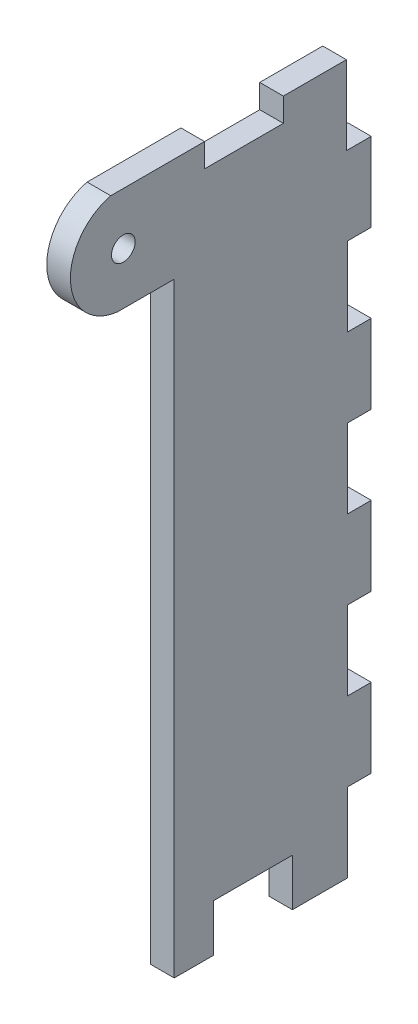
SolidWorks part; units mm, degrees
ref_plane "Front Plane" through (0, 0, 0) normal (0, 0, 1) x (1, 0, 0)
ref_plane "Top Plane" through (0, 0, 0) normal (0, 1, 0) x (1, 0, 0)
ref_plane "Right Plane" through (0, 0, 0) normal (1, 0, 0) x (0, 0, -1)
sketch "Sketch1" plane through (0, 0, 0) normal (1, 0, 0) x (0, 0, -1)
  line L0 (-9.3817, 95.693) -> (-1.0642, 95.693)
  line L1 (-1.3244, 5.693) -> (3.6756, 5.693)
  line L2 (-1.3244, 5.693) -> (-1.3244, 82.493)
  line L3 (-1.0642, 95.693) -> (2.5257, 95.693)
  line L4 (23.6756, 15.693) -> (23.6756, 25.693)
  line L5 (3.6756, 11.693) -> (13.6756, 11.693)
  line L6 (3.6756, 11.693) -> (3.6756, 5.693)
  line L8 (13.6756, 11.693) -> (13.6756, 5.693)
  line L9 (20.6756, 15.693) -> (23.6756, 15.693)
  line L10 (20.6756, 15.693) -> (20.6756, 5.693)
  line L11 (13.6756, 5.693) -> (20.6756, 5.693)
  line L13 (20.6756, 35.693) -> (23.6756, 35.693)
  line L14 (20.6756, 35.693) -> (20.6756, 25.693)
  line L15 (20.6756, 25.693) -> (23.6756, 25.693)
  line L17 (20.6756, 55.693) -> (23.6756, 55.693)
  line L18 (20.6756, 55.693) -> (20.6756, 45.693)
  line L19 (20.6756, 45.693) -> (23.6756, 45.693)
  line L20 (23.6756, 35.693) -> (23.6756, 45.693)
  line L21 (20.6756, 75.693) -> (23.6756, 75.693)
  line L22 (20.6756, 75.693) -> (20.6756, 65.693)
  line L23 (20.6756, 65.693) -> (23.6756, 65.693)
  line L24 (23.6756, 55.693) -> (23.6756, 65.693)
  line L26 (20.5257, 95.693) -> (20.5257, 85.693)
  line L27 (20.5257, 85.693) -> (23.6756, 85.693)
  line L28 (23.6756, 75.693) -> (23.6756, 85.693)
  line L29 (12.5257, 92.693) -> (2.5257, 92.693)
  line L30 (12.5257, 92.693) -> (12.5257, 95.693)
  line L32 (2.5257, 92.693) -> (2.5257, 95.693)
  line L33 (-1.3244, 82.493) -> (-8.482, 82.493)
  line L34 (12.5257, 95.693) -> (20.5257, 95.693)
  circle A0 centre (-7.7836, 89.093) radius 1.5
  arc A1 (-9.3817, 95.693) -> (-8.482, 82.493) centre (-7.7802, 89.1715) ccw
  dimension "D1" = 76.8
  dimension "D2" = 3
  dimension "D3" = 6
  dimension "D4" = 10
  dimension "D5" = 10
  dimension "D6" = 10
  dimension "D7" = 10
  dimension "D8" = 10
  dimension "D9" = 10
  dimension "D10" = 10
  dimension "D11" = 3
  dimension "D12" = 3
  dimension "D13" = 3
  dimension "D14" = 3
  dimension "D15" = 3
  dimension "D16" = 10
  dimension "D17" = 8
  dimension "D18" = 10
  dimension "D19" = 5
  dimension "D20" = 7
  dimension "D21" = 10
  dimension "D22" = 6.6
  dimension "D23" = 6.6
extrude "Boss-Extrude1" add sketch "Sketch1" along normal blind 3
